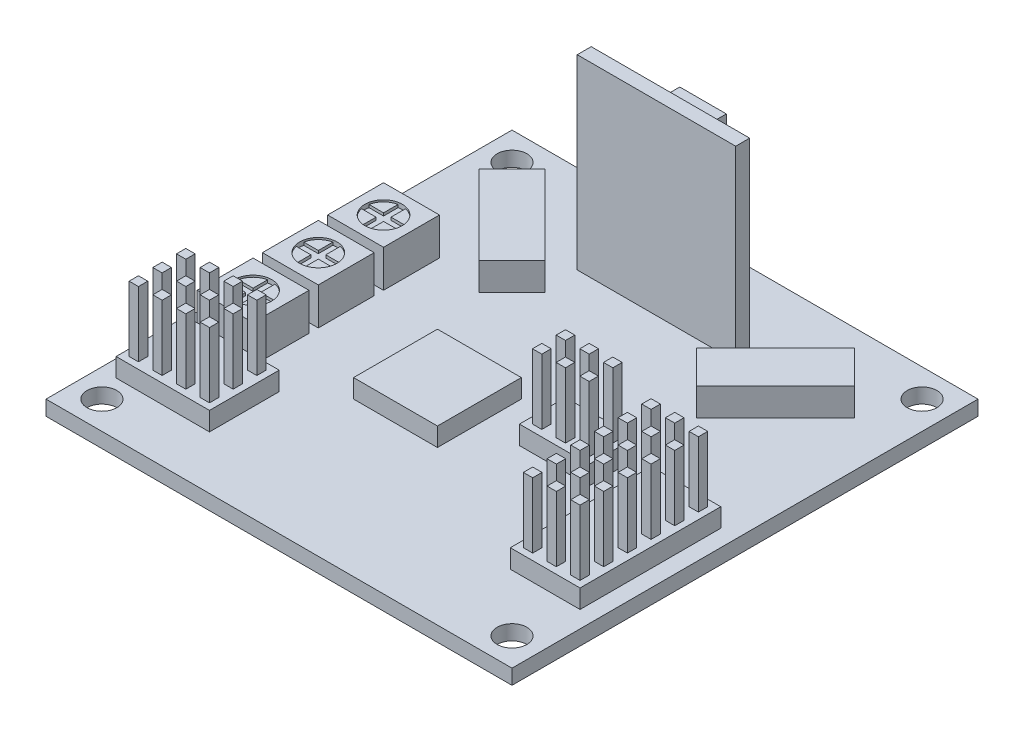
SolidWorks part; units mm, degrees
ref_plane "Front Plane" through (0, 0, 0) normal (0, 0, 1) x (1, 0, 0)
ref_plane "Top Plane" through (0, 0, 0) normal (0, 1, 0) x (1, 0, 0)
ref_plane "Right Plane" through (0, 0, 0) normal (1, 0, 0) x (0, 0, -1)
sketch "Sketch1" plane through (0, 0, 0) normal (0, 1, 0) x (1, 0, 0)
  line L1 (-25, -25) -> (25, -25)
  line L2 (-25, -25) -> (-25, 25)
  line L3 (-25, 25) -> (25, 25)
  line L4 (25, -25) -> (25, 25)
  line L5 (-25, -25) -> (25, 25) construction
  line L6 (-25, 25) -> (25, -25) construction
  circle A0 centre (-22, 22) radius 1.6
  circle A1 centre (22, 22) radius 1.6
  circle A2 centre (22, -22) radius 1.6
  circle A3 centre (-22, -22) radius 1.6
  point P0 (0, 0)
  point P17 (0, 0)
  dimension "D2" = 3.2
  dimension "D3" = 22
  dimension "D1" = 50
  dimension "D4" = 4
extrude "Boss-Extrude1" add sketch "Sketch1" along normal blind 1.6
sketch "Sketch2" plane through (0, 1.6, 0) normal (0, 1, 0) x (1, 0, 0)
  line L1 (-23, -3.7831) -> (-17, -3.7831)
  line L2 (-23, -3.7831) -> (-23, 2.2169)
  line L3 (-23, 2.2169) -> (-17, 2.2169)
  line L4 (-17, -3.7831) -> (-17, 2.2169)
  line L5 (-23, -3.7831) -> (-17, 2.2169) construction
  line L6 (-23, 2.2169) -> (-17, -3.7831) construction
  line L7 (-23, 3.2169) -> (-17, 3.2169)
  line L8 (-23, 3.2169) -> (-23, 9.2169)
  line L9 (-23, 9.2169) -> (-17, 9.2169)
  line L10 (-17, 3.2169) -> (-17, 9.2169)
  line L11 (-23, 3.2169) -> (-17, 9.2169) construction
  line L12 (-23, 9.2169) -> (-17, 3.2169) construction
  line L13 (-23, -10.7831) -> (-17, -10.7831)
  line L14 (-23, -10.7831) -> (-23, -4.7831)
  line L15 (-23, -4.7831) -> (-17, -4.7831)
  line L16 (-17, -10.7831) -> (-17, -4.7831)
  line L17 (-23, -10.7831) -> (-17, -4.7831) construction
  line L18 (-23, -4.7831) -> (-17, -10.7831) construction
  point P0 (-20, -0.7831)
  point P5 (-20, 6.2169)
  point P10 (-20, -7.7831)
  dimension "D1" = 20
  dimension "D2" = 6
  dimension "D3" = 1
  dimension "D4" = 1
extrude "Boss-Extrude2" add sketch "Sketch2" along normal blind 4
sketch "Sketch3" plane through (0, 5.6, 0) normal (0, 1, 0) x (1, 0, 0)
  circle A0 centre (-20, 6.2169) radius 2
  circle A1 centre (-20, -0.7831) radius 2
  circle A2 centre (-20, -7.7831) radius 2
  dimension "D1" = 4
extrude "Cut-Extrude1" cut sketch "Sketch3" against normal blind 0.2
sketch "Sketch4" plane through (0, 5.6, 0) normal (0, 1, 0) x (1, 0, 0)
  line L0 (-21.9596, 6.6169) -> (-20.4, 6.6169)
  line L1 (-20.4, 6.6169) -> (-20.4, 8.1764)
  line L2 (-19.6, 8.1764) -> (-19.6, 6.6169)
  line L3 (-19.6, 6.6169) -> (-18.0404, 6.6169)
  line L4 (-18.0404, 5.8169) -> (-19.6, 5.8169)
  line L5 (-19.6, 5.8169) -> (-19.6, 4.2573)
  line L6 (-20.4, 4.2573) -> (-20.4, 5.8169)
  line L7 (-20.4, 5.8169) -> (-21.9596, 5.8169)
  line L8 (-21.9596, -0.3831) -> (-20.4, -0.3831)
  line L9 (-20.4, -0.3831) -> (-20.4, 1.1764)
  line L10 (-19.6, 1.1764) -> (-19.6, -0.3831)
  line L11 (-19.6, -0.3831) -> (-18.0404, -0.3831)
  line L12 (-18.0404, -1.1831) -> (-19.6, -1.1831)
  line L13 (-19.6, -1.1831) -> (-19.6, -2.7427)
  line L14 (-20.4, -2.7427) -> (-20.4, -1.1831)
  line L15 (-20.4, -1.1831) -> (-21.9596, -1.1831)
  line L16 (-21.9596, -7.3831) -> (-20.4, -7.3831)
  line L17 (-20.4, -7.3831) -> (-20.4, -5.8236)
  line L18 (-19.6, -5.8236) -> (-19.6, -7.3831)
  line L19 (-19.6, -7.3831) -> (-18.0404, -7.3831)
  line L20 (-18.0404, -8.1831) -> (-19.6, -8.1831)
  line L21 (-19.6, -8.1831) -> (-19.6, -9.7427)
  line L22 (-20.4, -9.7427) -> (-20.4, -8.1831)
  line L23 (-20.4, -8.1831) -> (-21.9596, -8.1831)
  circle A0 centre (-20, 6.2169) radius 2 construction
  arc A1 (-21.9596, 6.6169) -> (-21.9596, 5.8169) centre (-20, 6.2169) ccw
  arc A2 (-19.6, 8.1764) -> (-20.4, 8.1764) centre (-20, 6.2169) ccw
  circle A3 centre (-20, 6.2169) radius 2
  arc A4 (-21.9596, 6.6169) -> (-21.9596, 5.8169) centre (-20, 6.2169) ccw
  arc A5 (-19.6, 8.1764) -> (-20.4, 8.1764) centre (-20, 6.2169) ccw
  arc A6 (-18.0404, 5.8169) -> (-18.0404, 6.6169) centre (-20, 6.2169) ccw
  arc A7 (-18.0404, 5.8169) -> (-18.0404, 6.6169) centre (-20, 6.2169) ccw
  arc A8 (-20.4, 4.2573) -> (-19.6, 4.2573) centre (-20, 6.2169) ccw
  arc A9 (-20.4, 4.2573) -> (-19.6, 4.2573) centre (-20, 6.2169) ccw
  arc A10 (-21.9596, -0.3831) -> (-21.9596, -1.1831) centre (-20, -0.7831) ccw
  arc A11 (-19.6, 1.1764) -> (-20.4, 1.1764) centre (-20, -0.7831) ccw
  arc A12 (-21.9596, -0.3831) -> (-21.9596, -1.1831) centre (-20, -0.7831) ccw
  arc A13 (-19.6, 1.1764) -> (-20.4, 1.1764) centre (-20, -0.7831) ccw
  arc A14 (-18.0404, -1.1831) -> (-18.0404, -0.3831) centre (-20, -0.7831) ccw
  arc A15 (-18.0404, -1.1831) -> (-18.0404, -0.3831) centre (-20, -0.7831) ccw
  arc A16 (-20.4, -2.7427) -> (-19.6, -2.7427) centre (-20, -0.7831) ccw
  arc A17 (-20.4, -2.7427) -> (-19.6, -2.7427) centre (-20, -0.7831) ccw
  arc A18 (-21.9596, -7.3831) -> (-21.9596, -8.1831) centre (-20, -7.7831) ccw
  arc A19 (-19.6, -5.8236) -> (-20.4, -5.8236) centre (-20, -7.7831) ccw
  arc A20 (-21.9596, -7.3831) -> (-21.9596, -8.1831) centre (-20, -7.7831) ccw
  arc A21 (-19.6, -5.8236) -> (-20.4, -5.8236) centre (-20, -7.7831) ccw
  arc A22 (-18.0404, -8.1831) -> (-18.0404, -7.3831) centre (-20, -7.7831) ccw
  arc A23 (-18.0404, -8.1831) -> (-18.0404, -7.3831) centre (-20, -7.7831) ccw
  arc A24 (-20.4, -9.7427) -> (-19.6, -9.7427) centre (-20, -7.7831) ccw
  arc A25 (-20.4, -9.7427) -> (-19.6, -9.7427) centre (-20, -7.7831) ccw
  point P21 (-20, 6.2169)
  point P33 (-20, -0.7831)
  point P48 (-20, -7.7831)
  circle M10 centre (-20, 6.2169) radius 2
  dimension "D3" = 0.8
  dimension "D1" = 0
  dimension "D4" = 3
  dimension "D2" = 4
extrude "Cut-Extrude2" cut sketch "Sketch4" against normal blind 0.5 contours L7 L6 L5 L4 L3 L2 L1 L0 M10 | L14 A16 L13 L12 A14 L11 L10 A11 L9 L8 A10 L15 | L22 A24 L21 L20 A22 L19 L18 A19 L17 L16 A18 L23
sketch "Sketch5" plane through (0, 1.6, 0) normal (0, 1, 0) x (1, 0, 0)
  line L0 (25, 25) -> (-25, 25) construction
  line L1 (-8.5, 15.5) -> (8.5, 15.5)
  line L2 (-8.5, 15.5) -> (-8.5, 17)
  line L3 (-8.5, 17) -> (8.5, 17)
  line L4 (8.5, 15.5) -> (8.5, 17)
  line L5 (-8.5, 15.5) -> (8.5, 17) construction
  line L6 (-8.5, 17) -> (8.5, 15.5) construction
  point P0 (0, 16.25)
  dimension "D1" = 17
  dimension "D2" = 0
  dimension "D3" = 8
  dimension "D4" = 1.5
extrude "Boss-Extrude3" add sketch "Sketch5" along normal blind 20
sketch "Sketch6" plane through (0, 1.6, 0) normal (0, 1, 0) x (1, 0, 0)
  line L0 (8.5, 17) -> (-8.5, 17) construction
  line L1 (-5.08, 18.5) -> (5.08, 18.5)
  line L2 (-5.08, 18.5) -> (-5.08, 15.5)
  line L3 (-5.08, 15.5) -> (5.08, 15.5)
  line L4 (5.08, 18.5) -> (5.08, 15.5)
  line L5 (-5.08, 18.5) -> (5.08, 15.5) construction
  line L6 (-5.08, 15.5) -> (5.08, 18.5) construction
  line L7 (-8.5, 15.5) -> (8.5, 15.5) construction
  point P0 (0, 17)
  dimension "D1" = 10.16
extrude "Boss-Extrude4" add sketch "Sketch6" along normal blind 2
sketch "Sketch7" plane through (0, 1.6, 0) normal (0, 1, 0) x (1, 0, 0)
  line L0 (0, 0) -> (-22, 22) construction
  line L1 (0, 0) -> (0, 25) construction
  line L2 (25, 25) -> (-25, 25) construction
  line L3 (-20.1525, 16.617) -> (-11.6673, 8.1317)
  line L4 (-20.1525, 16.617) -> (-16.617, 20.1525)
  line L5 (-11.6673, 8.1317) -> (-8.1317, 11.6673)
  line L6 (-16.617, 20.1525) -> (-8.1317, 11.6673)
  line L7 (-20.1525, 16.617) -> (-8.1317, 11.6673) construction
  line L8 (-11.6673, 8.1317) -> (-16.617, 20.1525) construction
  line L9 (11.6673, 8.1317) -> (16.617, 20.1525) construction
  line L10 (20.1525, 16.617) -> (8.1317, 11.6673) construction
  line L11 (16.617, 20.1525) -> (8.1317, 11.6673)
  line L12 (11.6673, 8.1317) -> (8.1317, 11.6673)
  line L13 (20.1525, 16.617) -> (16.617, 20.1525)
  line L14 (20.1525, 16.617) -> (11.6673, 8.1317)
  point P8 (-14.1421, 14.1421)
  point P16 (14.1421, 14.1421)
  dimension "D1" = 5
  dimension "D2" = 12
  dimension "D3" = 20
extrude "Boss-Extrude5" add sketch "Sketch7" along normal blind 3
sketch "Sketch8" plane through (0, 0, -17) normal (0, 0, -1) x (-1, 0, 0)
  line L0 (-8.5, 21.6) -> (-8.5, 1.6) construction
  line L1 (-3, 7.6) -> (2, 7.6)
  line L2 (-3, 7.6) -> (-3, 19.6)
  line L3 (-3, 19.6) -> (2, 19.6)
  line L4 (2, 7.6) -> (2, 19.6)
  line L5 (-3, 7.6) -> (2, 19.6) construction
  line L6 (-3, 19.6) -> (2, 7.6) construction
  line L7 (-8.5, 21.6) -> (8.5, 21.6) construction
  point P0 (-0.5, 13.6)
  dimension "D1" = 5
  dimension "D2" = 12
  dimension "D3" = 8
  dimension "D4" = 2
extrude "Boss-Extrude6" add sketch "Sketch8" along normal blind 3
sketch "Sketch9" plane through (0, 1.6, 0) normal (0, 1, 0) x (1, 0, 0)
  line L1 (-8.5, -8.5) -> (0.5, -8.5)
  line L2 (-8.5, -8.5) -> (-8.5, 0.5)
  line L3 (-8.5, 0.5) -> (0.5, 0.5)
  line L4 (0.5, -8.5) -> (0.5, 0.5)
  line L5 (-8.5, -8.5) -> (0.5, 0.5) construction
  line L6 (-8.5, 0.5) -> (0.5, -8.5) construction
  point P0 (-4, -4)
  dimension "D1" = 9
  dimension "D2" = 4
  dimension "D3" = 4
extrude "Boss-Extrude7" add sketch "Sketch9" along normal blind 2
sketch "Sketch10" plane through (0, 1.6, 0) normal (0, 1, 0) x (1, 0, 0)
  line L0 (-19.96, -13.5) -> (-18.96, -13.5)
  line L1 (-22.5, -13.5) -> (-21.5, -13.5)
  line L2 (-22.5, -13.5) -> (-22.5, -12.5)
  line L3 (-22.5, -12.5) -> (-21.5, -12.5)
  line L4 (-21.5, -13.5) -> (-21.5, -12.5)
  line L5 (-22.5, -13.5) -> (-21.5, -12.5) construction
  line L6 (-22.5, -12.5) -> (-21.5, -13.5) construction
  line L7 (-19.96, -13.5) -> (-19.96, -12.5)
  line L8 (-19.96, -12.5) -> (-18.96, -12.5)
  line L9 (-18.96, -13.5) -> (-18.96, -12.5)
  line L10 (-19.96, -13.5) -> (-18.96, -12.5) construction
  line L11 (-19.96, -12.5) -> (-18.96, -13.5) construction
  line L12 (-17.42, -13.5) -> (-16.42, -13.5)
  line L13 (-17.42, -13.5) -> (-17.42, -12.5)
  line L14 (-17.42, -12.5) -> (-16.42, -12.5)
  line L15 (-16.42, -13.5) -> (-16.42, -12.5)
  line L16 (-17.42, -13.5) -> (-16.42, -12.5) construction
  line L17 (-17.42, -12.5) -> (-16.42, -13.5) construction
  line L18 (-14.88, -13.5) -> (-13.88, -13.5)
  line L19 (-14.88, -13.5) -> (-14.88, -12.5)
  line L20 (-14.88, -12.5) -> (-13.88, -12.5)
  line L21 (-13.88, -13.5) -> (-13.88, -12.5)
  line L22 (-14.88, -13.5) -> (-13.88, -12.5) construction
  line L23 (-14.88, -12.5) -> (-13.88, -13.5) construction
  line L24 (-19.96, -16.04) -> (-18.96, -16.04)
  line L25 (-19.96, -16.04) -> (-19.96, -15.04)
  line L26 (-19.96, -15.04) -> (-18.96, -15.04)
  line L27 (-18.96, -16.04) -> (-18.96, -15.04)
  line L28 (-19.96, -16.04) -> (-18.96, -15.04) construction
  line L29 (-19.96, -15.04) -> (-18.96, -16.04) construction
  line L30 (-17.42, -16.04) -> (-16.42, -16.04)
  line L31 (-17.42, -16.04) -> (-17.42, -15.04)
  line L32 (-17.42, -15.04) -> (-16.42, -15.04)
  line L33 (-16.42, -16.04) -> (-16.42, -15.04)
  line L34 (-17.42, -16.04) -> (-16.42, -15.04) construction
  line L35 (-17.42, -15.04) -> (-16.42, -16.04) construction
  line L36 (-14.88, -16.04) -> (-13.88, -16.04)
  line L37 (-14.88, -16.04) -> (-14.88, -15.04)
  line L38 (-14.88, -15.04) -> (-13.88, -15.04)
  line L39 (-13.88, -16.04) -> (-13.88, -15.04)
  line L40 (-14.88, -16.04) -> (-13.88, -15.04) construction
  line L41 (-14.88, -15.04) -> (-13.88, -16.04) construction
  line L42 (-19.96, -18.58) -> (-18.96, -18.58)
  line L43 (-19.96, -18.58) -> (-19.96, -17.58)
  line L44 (-19.96, -17.58) -> (-18.96, -17.58)
  line L45 (-18.96, -18.58) -> (-18.96, -17.58)
  line L46 (-19.96, -18.58) -> (-18.96, -17.58) construction
  line L47 (-19.96, -17.58) -> (-18.96, -18.58) construction
  line L48 (-17.42, -18.58) -> (-16.42, -18.58)
  line L49 (-17.42, -18.58) -> (-17.42, -17.58)
  line L50 (-17.42, -17.58) -> (-16.42, -17.58)
  line L51 (-16.42, -18.58) -> (-16.42, -17.58)
  line L52 (-17.42, -18.58) -> (-16.42, -17.58) construction
  line L53 (-17.42, -17.58) -> (-16.42, -18.58) construction
  line L54 (-14.88, -18.58) -> (-13.88, -18.58)
  line L55 (-14.88, -18.58) -> (-14.88, -17.58)
  line L56 (-14.88, -17.58) -> (-13.88, -17.58)
  line L57 (-13.88, -18.58) -> (-13.88, -17.58)
  line L58 (-14.88, -18.58) -> (-13.88, -17.58) construction
  line L59 (-14.88, -17.58) -> (-13.88, -18.58) construction
  line L60 (-22.5, -16.04) -> (-21.5, -16.04)
  line L61 (-22.5, -16.04) -> (-22.5, -15.04)
  line L62 (-22.5, -15.04) -> (-21.5, -15.04)
  line L63 (-21.5, -16.04) -> (-21.5, -15.04)
  line L64 (-22.5, -16.04) -> (-21.5, -15.04) construction
  line L65 (-22.5, -15.04) -> (-21.5, -16.04) construction
  line L66 (-22.5, -18.58) -> (-21.5, -18.58)
  line L67 (-22.5, -18.58) -> (-22.5, -17.58)
  line L68 (-22.5, -17.58) -> (-21.5, -17.58)
  line L69 (-21.5, -18.58) -> (-21.5, -17.58)
  line L70 (-22.5, -18.58) -> (-21.5, -17.58) construction
  line L71 (-22.5, -17.58) -> (-21.5, -18.58) construction
  line L72 (-25, -25) -> (25, -25) construction
  line L73 (-25, 25) -> (-25, -25) construction
  line L74 (25, -25) -> (25, 25) construction
  line L75 (21.5, -2.5) -> (22.5, -2.5)
  line L76 (21.5, -2.5) -> (21.5, -1.5)
  line L77 (21.5, -1.5) -> (22.5, -1.5)
  line L78 (22.5, -2.5) -> (22.5, -1.5)
  line L79 (21.5, -2.5) -> (22.5, -1.5) construction
  line L80 (21.5, -1.5) -> (22.5, -2.5) construction
  line L81 (18.96, -2.5) -> (19.96, -2.5)
  line L82 (18.96, -2.5) -> (18.96, -1.5)
  line L83 (18.96, -1.5) -> (19.96, -1.5)
  line L84 (19.96, -2.5) -> (19.96, -1.5)
  line L85 (18.96, -2.5) -> (19.96, -1.5) construction
  line L86 (18.96, -1.5) -> (19.96, -2.5) construction
  line L87 (16.42, -2.5) -> (17.42, -2.5)
  line L88 (16.42, -2.5) -> (16.42, -1.5)
  line L89 (16.42, -1.5) -> (17.42, -1.5)
  line L90 (17.42, -2.5) -> (17.42, -1.5)
  line L91 (16.42, -2.5) -> (17.42, -1.5) construction
  line L92 (16.42, -1.5) -> (17.42, -2.5) construction
  line L93 (18.96, -5.04) -> (19.96, -5.04)
  line L94 (18.96, -5.04) -> (18.96, -4.04)
  line L95 (18.96, -4.04) -> (19.96, -4.04)
  line L96 (19.96, -5.04) -> (19.96, -4.04)
  line L97 (18.96, -5.04) -> (19.96, -4.04) construction
  line L98 (18.96, -4.04) -> (19.96, -5.04) construction
  line L99 (16.42, -5.04) -> (17.42, -5.04)
  line L100 (16.42, -5.04) -> (16.42, -4.04)
  line L101 (16.42, -4.04) -> (17.42, -4.04)
  line L102 (17.42, -5.04) -> (17.42, -4.04)
  line L103 (16.42, -5.04) -> (17.42, -4.04) construction
  line L104 (16.42, -4.04) -> (17.42, -5.04) construction
  line L105 (18.96, -7.58) -> (19.96, -7.58)
  line L106 (18.96, -7.58) -> (18.96, -6.58)
  line L107 (18.96, -6.58) -> (19.96, -6.58)
  line L108 (19.96, -7.58) -> (19.96, -6.58)
  line L109 (18.96, -7.58) -> (19.96, -6.58) construction
  line L110 (18.96, -6.58) -> (19.96, -7.58) construction
  line L111 (16.42, -7.58) -> (17.42, -7.58)
  line L112 (16.42, -7.58) -> (16.42, -6.58)
  line L113 (16.42, -6.58) -> (17.42, -6.58)
  line L114 (17.42, -7.58) -> (17.42, -6.58)
  line L115 (16.42, -7.58) -> (17.42, -6.58) construction
  line L116 (16.42, -6.58) -> (17.42, -7.58) construction
  line L117 (18.96, -10.12) -> (19.96, -10.12)
  line L118 (18.96, -10.12) -> (18.96, -9.12)
  line L119 (18.96, -9.12) -> (19.96, -9.12)
  line L120 (19.96, -10.12) -> (19.96, -9.12)
  line L121 (18.96, -10.12) -> (19.96, -9.12) construction
  line L122 (18.96, -9.12) -> (19.96, -10.12) construction
  line L123 (16.42, -10.12) -> (17.42, -10.12)
  line L124 (16.42, -10.12) -> (16.42, -9.12)
  line L125 (16.42, -9.12) -> (17.42, -9.12)
  line L126 (17.42, -10.12) -> (17.42, -9.12)
  line L127 (16.42, -10.12) -> (17.42, -9.12) construction
  line L128 (16.42, -9.12) -> (17.42, -10.12) construction
  line L129 (18.96, -12.66) -> (19.96, -12.66)
  line L130 (18.96, -12.66) -> (18.96, -11.66)
  line L131 (18.96, -11.66) -> (19.96, -11.66)
  line L132 (19.96, -12.66) -> (19.96, -11.66)
  line L133 (18.96, -12.66) -> (19.96, -11.66) construction
  line L134 (18.96, -11.66) -> (19.96, -12.66) construction
  line L135 (16.42, -12.66) -> (17.42, -12.66)
  line L136 (16.42, -12.66) -> (16.42, -11.66)
  line L137 (16.42, -11.66) -> (17.42, -11.66)
  line L138 (17.42, -12.66) -> (17.42, -11.66)
  line L139 (16.42, -12.66) -> (17.42, -11.66) construction
  line L140 (16.42, -11.66) -> (17.42, -12.66) construction
  line L141 (18.96, -15.2) -> (19.96, -15.2)
  line L142 (18.96, -15.2) -> (18.96, -14.2)
  line L143 (18.96, -14.2) -> (19.96, -14.2)
  line L144 (19.96, -15.2) -> (19.96, -14.2)
  line L145 (18.96, -15.2) -> (19.96, -14.2) construction
  line L146 (18.96, -14.2) -> (19.96, -15.2) construction
  line L147 (16.42, -15.2) -> (17.42, -15.2)
  line L148 (16.42, -15.2) -> (16.42, -14.2)
  line L149 (16.42, -14.2) -> (17.42, -14.2)
  line L150 (17.42, -15.2) -> (17.42, -14.2)
  line L151 (16.42, -15.2) -> (17.42, -14.2) construction
  line L152 (16.42, -14.2) -> (17.42, -15.2) construction
  line L153 (21.5, -5.04) -> (22.5, -5.04)
  line L154 (21.5, -5.04) -> (21.5, -4.04)
  line L155 (21.5, -4.04) -> (22.5, -4.04)
  line L156 (22.5, -5.04) -> (22.5, -4.04)
  line L157 (21.5, -5.04) -> (22.5, -4.04) construction
  line L158 (21.5, -4.04) -> (22.5, -5.04) construction
  line L159 (21.5, -7.58) -> (22.5, -7.58)
  line L160 (21.5, -7.58) -> (21.5, -6.58)
  line L161 (21.5, -6.58) -> (22.5, -6.58)
  line L162 (22.5, -7.58) -> (22.5, -6.58)
  line L163 (21.5, -7.58) -> (22.5, -6.58) construction
  line L164 (21.5, -6.58) -> (22.5, -7.58) construction
  line L165 (21.5, -10.12) -> (22.5, -10.12)
  line L166 (21.5, -10.12) -> (21.5, -9.12)
  line L167 (21.5, -9.12) -> (22.5, -9.12)
  line L168 (22.5, -10.12) -> (22.5, -9.12)
  line L169 (21.5, -10.12) -> (22.5, -9.12) construction
  line L170 (21.5, -9.12) -> (22.5, -10.12) construction
  line L171 (21.5, -12.66) -> (22.5, -12.66)
  line L172 (21.5, -12.66) -> (21.5, -11.66)
  line L173 (21.5, -11.66) -> (22.5, -11.66)
  line L174 (22.5, -12.66) -> (22.5, -11.66)
  line L175 (21.5, -12.66) -> (22.5, -11.66) construction
  line L176 (21.5, -11.66) -> (22.5, -12.66) construction
  line L177 (21.5, -15.2) -> (22.5, -15.2)
  line L178 (21.5, -15.2) -> (21.5, -14.2)
  line L179 (21.5, -14.2) -> (22.5, -14.2)
  line L180 (22.5, -15.2) -> (22.5, -14.2)
  line L181 (21.5, -15.2) -> (22.5, -14.2) construction
  line L182 (21.5, -14.2) -> (22.5, -15.2) construction
  line L183 (7.96, -0.6823) -> (8.96, -0.6823)
  line L184 (10.5, -0.6823) -> (11.5, -0.6823)
  line L185 (10.5, -0.6823) -> (10.5, 0.3177)
  line L186 (10.5, 0.3177) -> (11.5, 0.3177)
  line L187 (11.5, -0.6823) -> (11.5, 0.3177)
  line L188 (10.5, -0.6823) -> (11.5, 0.3177) construction
  line L189 (10.5, 0.3177) -> (11.5, -0.6823) construction
  line L190 (7.96, -0.6823) -> (7.96, 0.3177)
  line L191 (7.96, 0.3177) -> (8.96, 0.3177)
  line L192 (8.96, -0.6823) -> (8.96, 0.3177)
  line L193 (7.96, -0.6823) -> (8.96, 0.3177) construction
  line L194 (7.96, 0.3177) -> (8.96, -0.6823) construction
  line L195 (5.42, -0.6823) -> (6.42, -0.6823)
  line L196 (5.42, -0.6823) -> (5.42, 0.3177)
  line L197 (5.42, 0.3177) -> (6.42, 0.3177)
  line L198 (6.42, -0.6823) -> (6.42, 0.3177)
  line L199 (5.42, -0.6823) -> (6.42, 0.3177) construction
  line L200 (5.42, 0.3177) -> (6.42, -0.6823) construction
  line L201 (7.96, -3.2223) -> (8.96, -3.2223)
  line L202 (7.96, -3.2223) -> (7.96, -2.2223)
  line L203 (7.96, -2.2223) -> (8.96, -2.2223)
  line L204 (8.96, -3.2223) -> (8.96, -2.2223)
  line L205 (7.96, -3.2223) -> (8.96, -2.2223) construction
  line L206 (7.96, -2.2223) -> (8.96, -3.2223) construction
  line L207 (5.42, -3.2223) -> (6.42, -3.2223)
  line L208 (5.42, -3.2223) -> (5.42, -2.2223)
  line L209 (5.42, -2.2223) -> (6.42, -2.2223)
  line L210 (6.42, -3.2223) -> (6.42, -2.2223)
  line L211 (5.42, -3.2223) -> (6.42, -2.2223) construction
  line L212 (5.42, -2.2223) -> (6.42, -3.2223) construction
  line L213 (10.5, -3.2223) -> (11.5, -3.2223)
  line L214 (10.5, -3.2223) -> (10.5, -2.2223)
  line L215 (10.5, -2.2223) -> (11.5, -2.2223)
  line L216 (11.5, -3.2223) -> (11.5, -2.2223)
  line L217 (10.5, -3.2223) -> (11.5, -2.2223) construction
  line L218 (10.5, -2.2223) -> (11.5, -3.2223) construction
  point P0 (-22, -13)
  point P8 (-19.46, -13)
  point P13 (-16.92, -13)
  point P18 (-14.38, -13)
  point P23 (-19.46, -15.54)
  point P28 (-16.92, -15.54)
  point P33 (-14.38, -15.54)
  point P38 (-19.46, -18.08)
  point P43 (-16.92, -18.08)
  point P48 (-14.38, -18.08)
  point P53 (-22, -15.54)
  point P58 (-22, -18.08)
  point P64 (22, -2)
  point P71 (11, -0.1823)
  point P73 (19.46, -2)
  point P78 (16.92, -2)
  point P83 (19.46, -4.54)
  point P88 (16.92, -4.54)
  point P93 (19.46, -7.08)
  point P98 (16.92, -7.08)
  point P103 (19.46, -9.62)
  point P108 (16.92, -9.62)
  point P113 (19.46, -12.16)
  point P118 (16.92, -12.16)
  point P123 (19.46, -14.7)
  point P128 (16.92, -14.7)
  point P133 (22, -4.54)
  point P138 (22, -7.08)
  point P143 (22, -9.62)
  point P148 (22, -12.16)
  point P153 (22, -14.7)
  point P165 (8.46, -0.1823)
  point P170 (5.92, -0.1823)
  point P175 (8.46, -2.7223)
  point P180 (5.92, -2.7223)
  point P185 (11, -2.7223)
  dimension "D1" = 1
  dimension "D2" = 1
  dimension "D5" = 12
  dimension "D6" = 3
  dimension "D7" = 3
  dimension "D10" = 2
  dimension "D11" = 14
  dimension "D3" = 4
  dimension "D4" = 3
  dimension "D8" = 3
  dimension "D9" = 6
  dimension "D12" = 3
  dimension "D13" = 2
extrude "Boss-Extrude8" add sketch "Sketch10" along normal blind 9
sketch "Sketch11" plane through (0, 1.6, 0) normal (0, 1, 0) x (1, 0, 0)
  line L0 (-21.5, -12.5) -> (-22.5, -12.5) construction
  line L1 (-23.2, -11.8) -> (-13.18, -11.8)
  line L2 (-23.2, -11.8) -> (-23.2, -19.28)
  line L3 (-23.2, -19.28) -> (-13.18, -19.28)
  line L4 (-13.18, -11.8) -> (-13.18, -19.28)
  line L5 (-22.5, -12.5) -> (-22.5, -13.5) construction
  line L6 (-14.88, -18.58) -> (-13.88, -18.58) construction
  line L7 (-13.88, -18.58) -> (-13.88, -17.58) construction
  line L8 (5.42, 0.3177) -> (5.42, -0.6823) construction
  line L9 (4.72, -3.9223) -> (12.2, -3.9223)
  line L10 (4.72, -3.9223) -> (4.72, 1.0177)
  line L11 (4.72, 1.0177) -> (12.2, 1.0177)
  line L12 (12.2, -3.9223) -> (12.2, 1.0177)
  line L13 (5.42, -3.2223) -> (6.42, -3.2223) construction
  line L14 (8.96, 0.3177) -> (7.96, 0.3177) construction
  line L15 (11.5, -0.6823) -> (11.5, 0.3177) construction
  line L16 (16.42, -1.5) -> (16.42, -2.5) construction
  line L17 (15.72, -0.8) -> (23.2, -0.8)
  line L18 (15.72, -0.8) -> (15.72, -15.9)
  line L19 (15.72, -15.9) -> (23.2, -15.9)
  line L20 (23.2, -0.8) -> (23.2, -15.9)
  line L21 (17.42, -1.5) -> (16.42, -1.5) construction
  line L22 (16.42, -15.2) -> (17.42, -15.2) construction
  line L23 (22.5, -15.2) -> (22.5, -14.2) construction
  point P6 (-22.5, -13)
  point P11 (-13.88, -18.08)
  point P18 (5.42, -0.1823)
  point P23 (8.46, 0.3177)
  point P32 (16.42, -2)
  point P37 (16.92, -15.2)
  point P40 (22.5, -14.7)
  dimension "D1" = 0.7
  dimension "D2" = 0.7
  dimension "D3" = 0.7
  dimension "D4" = 0.7
  dimension "D5" = 0.7
  dimension "D6" = 0.7
  dimension "D7" = 0.7
  dimension "D8" = 0.7
  dimension "D9" = 0.7
  dimension "D10" = 0.7
  dimension "D11" = 0.7
  dimension "D12" = 0.7
extrude "Boss-Extrude10" add sketch "Sketch11" along normal blind 2
